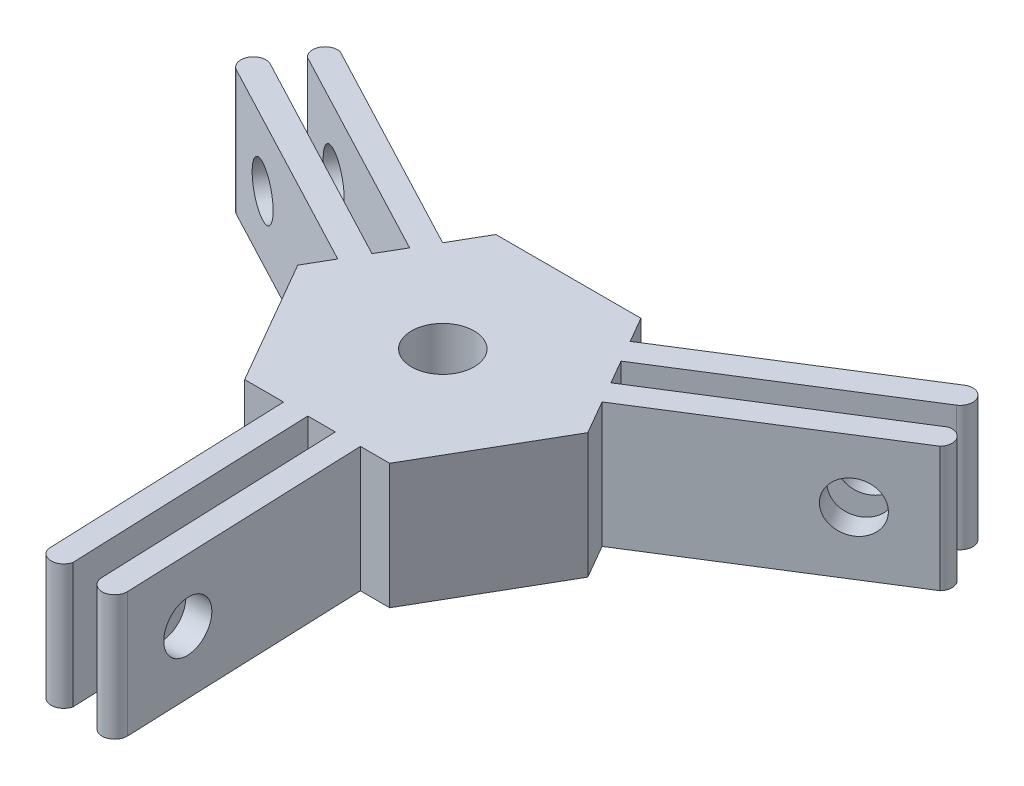
SolidWorks part; units mm, degrees
ref_plane "Front Plane" through (0, 0, 0) normal (0, 0, 1) x (1, 0, 0)
ref_plane "Top Plane" through (0, 0, 0) normal (0, 1, 0) x (1, 0, 0)
ref_plane "Right Plane" through (0, 0, 0) normal (1, 0, 0) x (0, 0, -1)
sketch "Sketch1" plane through (0, 0, 0) normal (0, 1, 0) x (1, 0, 0)
  line L0 (0, 0) -> (2.1154, 1.3323) construction
  line L1 (3.4294, -9.3936) -> (4.1979, -29.3788)
  line L2 (6.4203, 7.6668) -> (23.3438, 18.3249)
  line L3 (7.8455, 6.2007) -> (24.4096, 16.6325)
  line L4 (1.4472, -9.8947) -> (2.1994, -29.4556)
  line L5 (9.6881, 2.4781) -> (26.6116, 13.1362)
  line L6 (9.0115, 4.3351) -> (25.582, 14.7709)
  line L7 (-0.7514, -9.9717) -> (0.001, -29.5402)
  line L8 (-2.698, -9.6292) -> (-1.9295, -29.6144)
  line L9 (-9.8498, 1.7268) -> (-27.5417, 11.0539)
  line L10 (-9.2927, 3.694) -> (-26.609, 12.8231)
  line L11 (-8.2601, 5.6366) -> (-25.583, 14.7692)
  line L12 (-6.9901, 7.1511) -> (-24.6821, 16.4782)
  arc A0 (6.4203, 7.6668) -> (-6.9901, 7.1511) centre (0, 0) ccw
  circle A1 centre (0, 0) radius 2.5
  arc A2 (2.1994, -29.4556) -> (4.1979, -29.3788) centre (3.1986, -29.4172) ccw
  arc A3 (24.4096, 16.6325) -> (23.3438, 18.3249) centre (23.8767, 17.4787) ccw
  arc A4 (0.001, -29.5402) -> (-1.9295, -29.6144) centre (-0.9742, -29.3189) cw
  arc A5 (25.582, 14.7709) -> (26.6116, 13.1362) centre (25.878, 13.8157) cw
  arc A6 (9.0115, 4.3351) -> (7.8455, 6.2007) centre (0, 0) ccw
  arc A7 (-26.609, 12.8231) -> (-27.5417, 11.0539) centre (-27.0754, 11.9385) ccw
  arc A8 (-25.583, 14.7692) -> (-24.6821, 16.4782) centre (-24.9038, 15.5031) cw
  arc A9 (-9.8498, 1.7268) -> (-2.698, -9.6292) centre (0, 0) ccw
  arc A10 (-8.2601, 5.6366) -> (-9.2927, 3.694) centre (0, 0) ccw
  arc A11 (-0.7514, -9.9717) -> (1.4472, -9.8947) centre (0, 0) ccw
  arc A12 (3.4294, -9.3936) -> (9.6881, 2.4781) centre (0, 0) ccw
  point P7 (15.6157, 12.3163)
  point P15 (17.8539, 8.7623)
  point P39 (0, 0)
  dimension "D1" = 20
  dimension "D2" = 5
  dimension "D3" = 2
  dimension "D4" = 20
  dimension "D5" = 2.2
  dimension "D6" = 3
extrude "Boss-Extrude1" add sketch "Sketch1" along normal blind 10
sketch "Sketch2" plane through (3.0637, 0, -0.1178) normal (0.9993, 0, -0.0384) x (-0.0384, 0, -0.9993)
  line L0 (-29.5184, 10) -> (-29.5184, 0) construction
  line L1 (-29.5184, 0) -> (-9.5184, 0) construction
  circle A0 centre (-24.5184, 5) radius 2
  dimension "D1" = 5
  dimension "D3" = 4
  dimension "D2" = 5
extrude "Cut-Extrude1" cut sketch "Sketch2" against normal blind 10
pattern_circular "CirPattern1" count 3 over 360 about axis through (0, 10, 0) along (0, -1, 0) of "Cut-Extrude1"
sketch "Sketch3" plane through (0, 10, 0) normal (0, 1, 0) x (1, 0, 0)
  line L1 (11.5902, 0) -> (5.7951, 10.0374)
  line L2 (5.7951, 10.0374) -> (-5.7951, 10.0374)
  line L3 (-5.7951, 10.0374) -> (-11.5902, 0)
  line L4 (-11.5902, 0) -> (-5.7951, -10.0374)
  line L5 (-5.7951, -10.0374) -> (5.7951, -10.0374)
  line L6 (5.7951, -10.0374) -> (11.5902, 0)
  circle A0 centre (0, 0) radius 10.0374 construction
  circle A1 centre (0, 0) radius 2.5
extrude "Boss-Extrude3" add sketch "Sketch3" against normal blind 10
